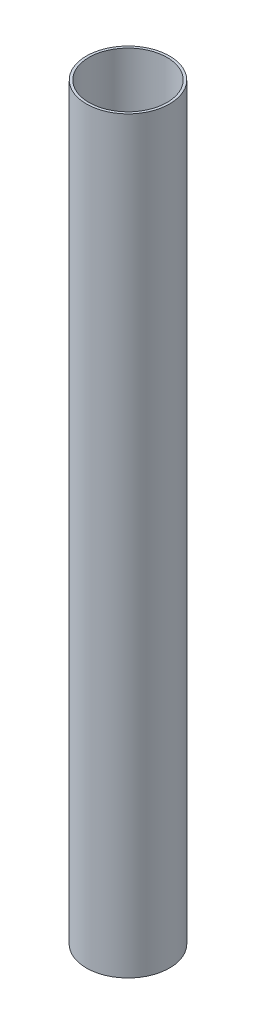
SolidWorks part; units mm, degrees
ref_plane "Front Plane" through (0, 0, 0) normal (0, 0, 1) x (1, 0, 0)
ref_plane "Top Plane" through (0, 0, 0) normal (0, 1, 0) x (1, 0, 0)
ref_plane "Right Plane" through (0, 0, 0) normal (1, 0, 0) x (0, 0, -1)
sketch "Sketch1" plane through (0, 0, 0) normal (0, 1, 0) x (1, 0, 0)
  circle A0 centre (0, 0) radius 6.35
  circle A1 centre (0, 0) radius 5.969
  dimension "D1" = 12.7
  dimension "D2" = 11.938
extrude "Boss-Extrude1" add sketch "Sketch1" along normal blind 114.3
